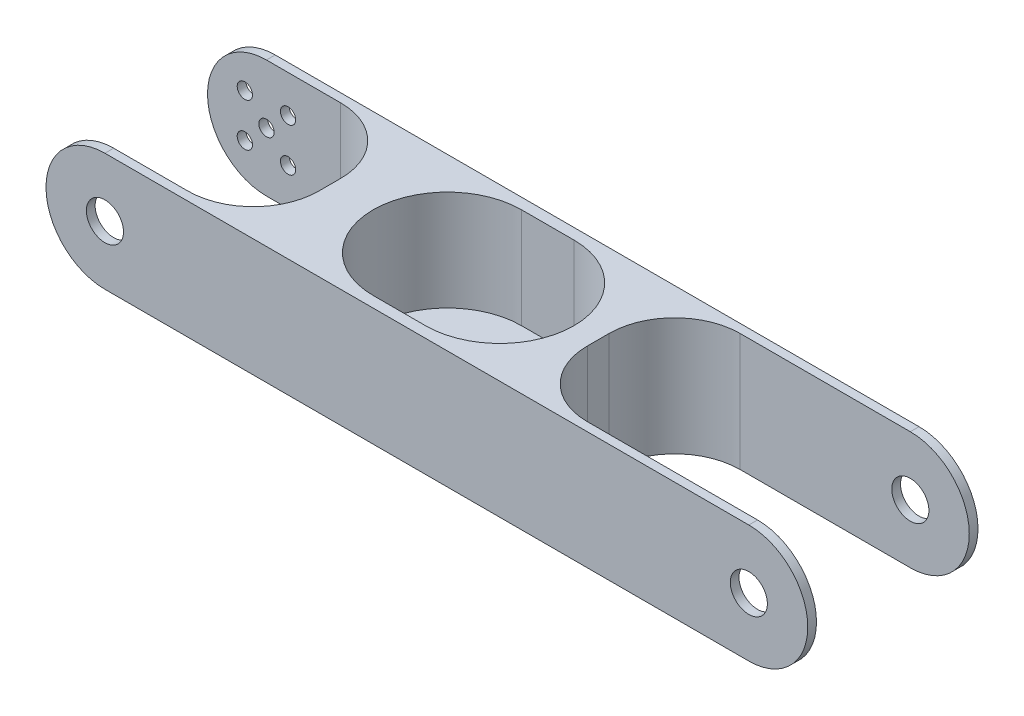
SolidWorks part; units mm, degrees
ref_plane "前视基准面" through (0, 0, 0) normal (0, 0, 1) x (1, 0, 0)
ref_plane "上视基准面" through (0, 0, 0) normal (0, 1, 0) x (1, 0, 0)
ref_plane "右视基准面" through (0, 0, 0) normal (1, 0, 0) x (0, 0, -1)
sketch "草图1" plane through (0, 0, 0) normal (0, 0, 1) x (1, 0, 0)
  line L0 (0, 0) -> (147.5, 0) construction
  line L1 (0, 13.5) -> (147.5, 13.5)
  line L2 (0, -13.5) -> (147.5, -13.5)
  arc A0 (0, 13.5) -> (0, -13.5) centre (0, 0) ccw
  arc A1 (147.5, -13.5) -> (147.5, 13.5) centre (147.5, 0) ccw
  point P3 (73.75, 0)
  dimension "D1" = 147.5
  dimension "D2" = 27
extrude "凸台-拉伸1" add sketch "草图1" along normal blind 39
sketch "草图2" plane through (0, 0, 39) normal (0, 0, 1) x (1, 0, 0)
  line L2 (0, -13.5) -> (147.5, -13.5)
  line L3 (147.5, 13.5) -> (0, 13.5)
  line L4 (0, -13.5) -> (147.5, -13.5)
  line L5 (147.5, 13.5) -> (0, 13.5)
  circle A1 centre (147.5, 0) radius 4.25
  arc A3 (0, 13.5) -> (0, -13.5) centre (0, 0) ccw
  arc A4 (147.5, -13.5) -> (147.5, 13.5) centre (147.5, 0) ccw
  arc A5 (0, 13.5) -> (0, -13.5) centre (0, 0) ccw
  arc A6 (147.5, -13.5) -> (147.5, 13.5) centre (147.5, 0) ccw
  dimension "D3" = 8.5
  dimension "D2" = 0
extrude "切除-拉伸2" cut sketch "草图2" against normal through all flip side to cut
sketch "草图5" plane through (0, 13.5, 0) normal (0, 1, 0) x (1, 0, 0)
  line L0 (0, -39) -> (0, 0) construction
  line L1 (-32, -37) -> (17, -37)
  line L2 (-32, -37) -> (-32, -2)
  line L3 (-32, -2) -> (17, -2)
  line L4 (32, -22) -> (32, -17)
  line L5 (-32, -37) -> (32, -2) construction
  line L6 (-32, -2) -> (32, -37) construction
  line L7 (147.5, 0) -> (0, 0) construction
  arc A0 (32, -22) -> (17, -37) centre (17, -22) cw
  arc A1 (17, -2) -> (32, -17) centre (17, -17) cw
  point P0 (0, -19.5)
  dimension "D3" = 15
  dimension "D4" = 15
  dimension "D1" = 2
  dimension "D2" = 32
extrude "切除-拉伸4" cut sketch "草图5" against normal through all
sketch "草图11" plane through (0, -13.5, 0) normal (0, -1, 0) x (1, 0, 0)
  line L0 (0, 39) -> (147.5, 39) construction
  line L1 (108.5, 37) -> (201.5, 37)
  line L2 (93.5, 22) -> (93.5, 17)
  line L3 (108.5, 2) -> (201.5, 2)
  line L4 (201.5, 37) -> (201.5, 2)
  line L5 (93.5, 37) -> (201.5, 2) construction
  line L6 (93.5, 2) -> (201.5, 37) construction
  line L7 (0, 0) -> (147.5, 0) construction
  line L8 (147.5, 39) -> (147.5, 0) construction
  arc A0 (108.5, 37) -> (93.5, 22) centre (108.5, 22) ccw
  arc A1 (108.5, 2) -> (93.5, 17) centre (108.5, 17) cw
  point P0 (147.5, 19.5)
  dimension "D4" = 15
  dimension "D5" = 15
  dimension "D1" = 2
  dimension "D2" = 2
  dimension "D3" = 54
extrude "切除-拉伸7" cut sketch "草图11" against normal through all
sketch "草图14" plane through (0, 13.5, 0) normal (0, 1, 0) x (1, 0, 0)
  line L0 (58.9448, -19.5) -> (70.9448, -19.5) construction
  line L1 (58.9448, -2.5) -> (70.9448, -2.5)
  line L2 (58.9448, -36.5) -> (70.9448, -36.5)
  line L3 (147.5, 0) -> (0, 0) construction
  line L4 (147.5, -39) -> (0, -39) construction
  arc A0 (58.9448, -2.5) -> (58.9448, -36.5) centre (58.9448, -19.5) ccw
  arc A1 (70.9448, -36.5) -> (70.9448, -2.5) centre (70.9448, -19.5) ccw
  point P2 (64.9448, -19.5)
  dimension "D3" = 6
  dimension "D1" = 2.5
  dimension "D2" = 2.5
extrude "切除-拉伸9" cut sketch "草图14" against normal offset from surface (23 mm away) 4 up to face at (68.25, -13.5, 19.5)
sketch "草图16" plane through (0, -13.5, 0) normal (0, -1, 0) x (1, 0, 0)
  line L0 (32, 19.5) -> (93.5, 19.5) construction
  line L1 (32, 22) -> (32, 17) construction
  line L2 (93.5, 22) -> (93.5, 17) construction
  line L3 (62, 19.5) -> (70, 19.5) construction
  line L12 (62, 29) -> (70, 29)
  line L13 (62, 10) -> (70, 10)
  line L14 (0, 0) -> (147.5, 0) construction
  arc A6 (62, 29) -> (62, 10) centre (62, 19.5) ccw
  arc A7 (70, 10) -> (70, 29) centre (70, 19.5) ccw
  point P8 (66, 19.5)
  point P18 (85.7427, 0)
  dimension "D1" = 10
  dimension "D2" = 8
  dimension "D3" = 30
extrude "切除-拉伸10" cut sketch "草图16" against normal through all
sketch "草图17" plane through (0, 0, 0) normal (0, 0, -1) x (-1, 0, 0)
  line L0 (4.9497, -4.9497) -> (-4.9497, 4.9497) construction
  line L1 (4.9497, -4.9497) -> (-4.9497, -4.9497) construction
  line L2 (4.9497, -4.9497) -> (4.9497, 4.9497) construction
  line L3 (4.9497, 4.9497) -> (-4.9497, 4.9497) construction
  line L4 (-4.9497, -4.9497) -> (-4.9497, 4.9497) construction
  line L5 (4.9497, -4.9497) -> (-4.9497, 4.9497) construction
  line L6 (4.9497, 4.9497) -> (-4.9497, -4.9497) construction
  line L7 (-4.9497, -4.9497) -> (4.9497, 4.9497) construction
  line L8 (-4.9497, 4.9497) -> (4.9497, -4.9497) construction
  circle A0 centre (0, 0) radius 1.75
  circle A1 centre (4.9497, 4.9497) radius 1.75
  circle A2 centre (0, 0) radius 1.75
  circle A3 centre (4.9497, -4.9497) radius 1.75
  circle A4 centre (0, 0) radius 1.75
  circle A5 centre (-4.9497, -4.9497) radius 1.75
  circle A6 centre (0, 0) radius 1.75
  circle A7 centre (-4.9497, 4.9497) radius 1.75
  point P23 (0, 0)
  dimension "D1" = 3.5
  dimension "D4" = 3.5
  dimension "D2" = 90
  dimension "D3" = 7
  dimension "D5" = 4
extrude "切除-拉伸13" cut sketch "草图17" against normal up to surface (2 mm away) contours A7 | A1 | A5 | A3 | A0 up to face at (5.125, 0, 2)
sketch "草图21" plane through (0, 0, 39) normal (0, 0, 1) x (1, 0, 0)
  circle A0 centre (0, 0) radius 4.25
  dimension "D1" = 8.5
extrude "切除-拉伸16" cut sketch "草图21" against normal up to next
